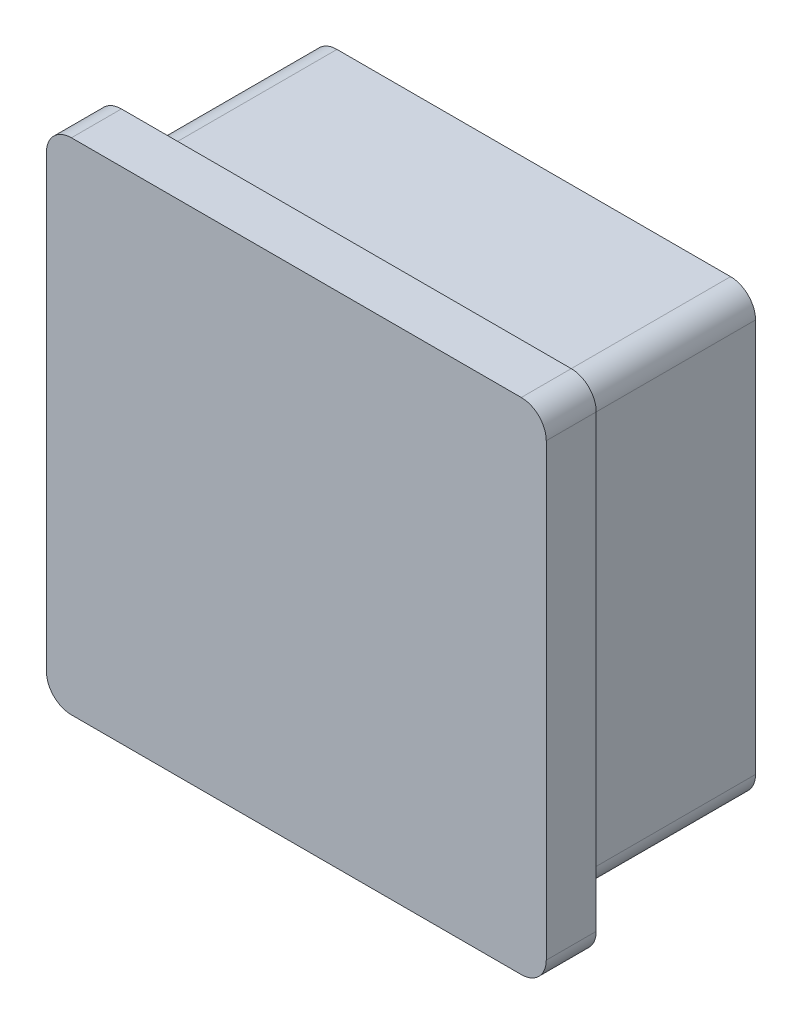
SolidWorks part; units mm, degrees
ref_plane "Přední rovina" through (0, 0, 0) normal (0, 0, 1) x (1, 0, 0)
ref_plane "Horní rovina" through (0, 0, 0) normal (0, 1, 0) x (1, 0, 0)
ref_plane "Pravá rovina" through (0, 0, 0) normal (1, 0, 0) x (0, 0, -1)
sketch "Skica1" plane through (0, 0, 0) normal (0, 0, 1) x (1, 0, 0)
  line L1 (-18, 20) -> (18, 20)
  line L2 (-20, 18) -> (-20, -18)
  line L3 (-18, -20) -> (18, -20)
  line L4 (20, 18) -> (20, -18)
  line L5 (-20, 20) -> (20, -20) construction
  line L6 (-20, -20) -> (20, 20) construction
  arc A0 (18, -20) -> (20, -18) centre (18, -18) ccw
  arc A1 (-20, -18) -> (-18, -20) centre (-18, -18) ccw
  arc A2 (-18, 20) -> (-20, 18) centre (-18, 18) ccw
  arc A3 (18, 20) -> (20, 18) centre (18, 18) cw
  point P0 (0, 0)
  dimension "D2" = 2
  dimension "D1" = 40
extrude "Přidat vysunutím1" add sketch "Skica1" along normal blind 4
sketch "Skica2" plane through (0, 0, 0) normal (0, 0, -1) x (-1, 0, 0)
  line L0 (-17.75, 15.75) -> (-17.75, -15.75)
  line L1 (15.25, 15.25) -> (-15.25, 15.25)
  line L2 (15.25, 15.25) -> (15.25, -15.25)
  line L3 (15.25, -15.25) -> (-15.25, -15.25)
  line L4 (-15.25, 15.25) -> (-15.25, -15.25)
  line L5 (15.25, 15.25) -> (-15.25, -15.25) construction
  line L6 (15.25, -15.25) -> (-15.25, 15.25) construction
  line L7 (15.75, -17.75) -> (-15.75, -17.75)
  line L8 (17.75, 15.75) -> (17.75, -15.75)
  line L9 (15.75, 17.75) -> (-15.75, 17.75)
  line L10 (15.25, 0) -> (-15.25, 0)
  line L11 (0, 15.25) -> (0, -15.25)
  line L12 (-11.25, 0) -> (-11.25, 4)
  line L13 (-11.25, 4) -> (-15.25, 4)
  line L14 (-11.25, 0) -> (-11.25, -4)
  line L15 (-11.25, -4) -> (-15.25, -4)
  line L16 (4, 11.25) -> (4, 15.25)
  line L17 (0, 11.25) -> (4, 11.25)
  line L18 (0, 11.25) -> (-4, 11.25)
  line L19 (-4, 11.25) -> (-4, 15.25)
  line L20 (11.25, -4) -> (15.25, -4)
  line L21 (11.25, 0) -> (11.25, -4)
  line L22 (11.25, 0) -> (11.25, 4)
  line L23 (11.25, 4) -> (15.25, 4)
  line L24 (-4, -11.25) -> (-4, -15.25)
  line L25 (0, -11.25) -> (-4, -11.25)
  line L26 (0, -11.25) -> (4, -11.25)
  line L27 (4, -11.25) -> (4, -15.25)
  line L28 (-17.75, 17.75) -> (-17.75, -17.75) construction
  line L29 (17.75, -17.75) -> (-17.75, -17.75) construction
  line L30 (17.75, 17.75) -> (17.75, -17.75) construction
  line L31 (17.75, 17.75) -> (-17.75, 17.75) construction
  arc A0 (-17.75, -15.75) -> (-15.75, -17.75) centre (-15.75, -15.75) ccw
  arc A1 (15.75, -17.75) -> (17.75, -15.75) centre (15.75, -15.75) ccw
  arc A2 (17.75, 15.75) -> (15.75, 17.75) centre (15.75, 15.75) ccw
  arc A3 (-17.75, 15.75) -> (-15.75, 17.75) centre (-15.75, 15.75) cw
  point P0 (0, 0)
  point P37 (0, 0)
  dimension "D6" = 2
  dimension "D1" = 30.5
  dimension "D3" = 4
  dimension "D4" = 4
  dimension "D2" = 2.5
  dimension "D5" = 4
extrude "Přidat vysunutím2" add sketch "Skica2" along normal blind 15 contours A3 L0 A0 L7 A1 L8 A2 L9 L4 L1 L2 L3 | L19 L18 L11 L1 | L11 L17 L16 L1 | L23 L22 L10 L2 | L10 L21 L20 L2 | L27 L26 L11 L3 | L11 L25 L24 L3 | L12 L13 L4 L10 | L15 L14 L10 L4
